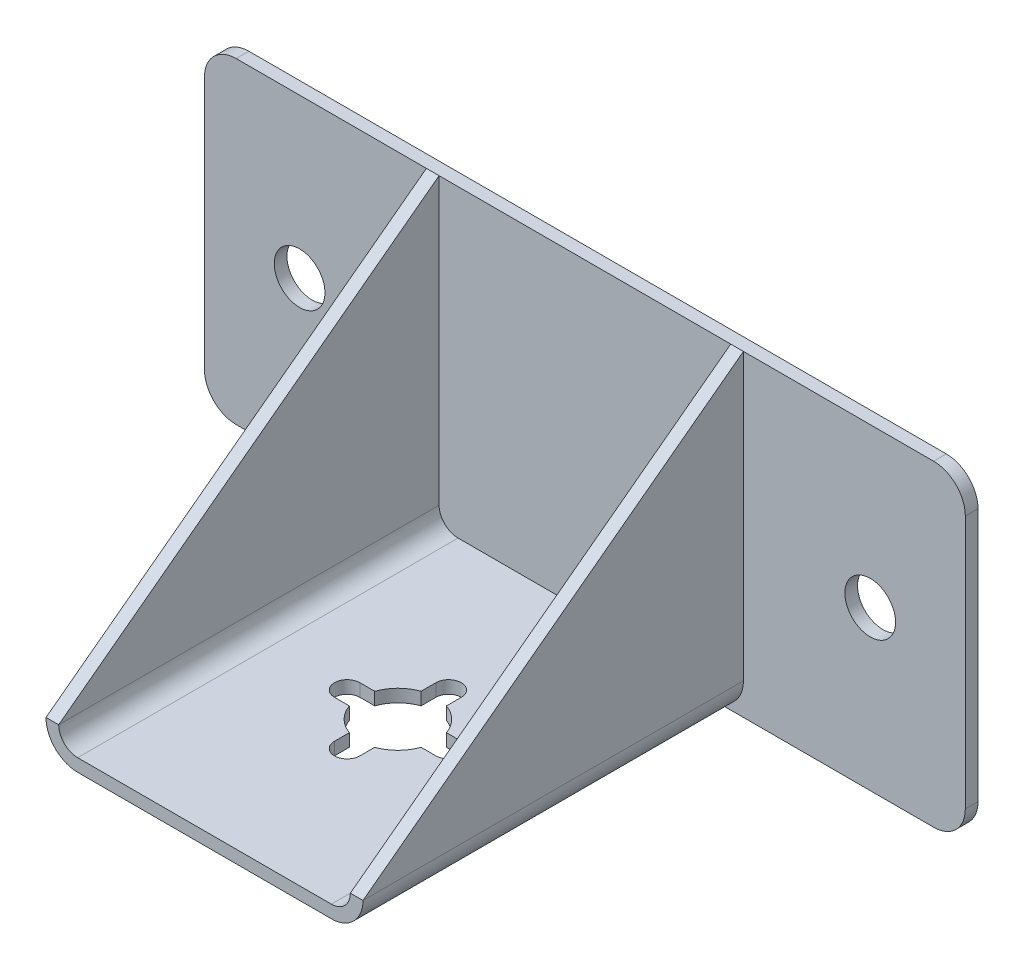
SolidWorks part; units mm, degrees
material "AISI 1020"
ref_plane "Alzado" through (0, 0, 0) normal (0, 0, 1) x (1, 0, 0)
ref_plane "Planta" through (0, 0, 0) normal (0, 1, 0) x (1, 0, 0)
ref_plane "Vista lateral" through (0, 0, 0) normal (1, 0, 0) x (0, 0, -1)
sketch "Croquis1" plane through (0, 0, 0) normal (0, 0, 1) x (1, 0, 0)
  line L1 (-55, -25) -> (55, -25)
  line L2 (-60, -20) -> (-60, 20)
  line L3 (-55, 25) -> (55, 25)
  line L4 (60, -20) -> (60, 20)
  line L5 (-60, -25) -> (60, 25) construction
  line L6 (-60, 25) -> (60, -25) construction
  arc A0 (55, 25) -> (60, 20) centre (55, 20) cw
  arc A1 (55, -25) -> (60, -20) centre (55, -20) ccw
  arc A2 (-55, -25) -> (-60, -20) centre (-55, -20) cw
  arc A3 (-60, 20) -> (-55, 25) centre (-55, 20) cw
  point P0 (0, 0)
  dimension "D3" = 5
  dimension "D1" = 120
  dimension "D2" = 50
extrude "Saliente-Extruir1" add sketch "Croquis1" along normal blind 2
sketch "Croquis2" plane through (0, 0, 2) normal (0, 0, 1) x (1, 0, 0)
  line L0 (55, 25) -> (-55, 25) construction
  line L1 (-20, -25) -> (20, -25)
  line L2 (-25, -20) -> (-25, 25)
  line L3 (-25, 25) -> (25, 25) construction
  line L4 (25, -20) -> (25, 25)
  line L5 (-25, -25) -> (25, 25) construction
  line L6 (-25, 25) -> (25, -25) construction
  line L7 (23, -20) -> (23, 25)
  line L8 (-20, -23) -> (20, -23)
  line L9 (-23, -20) -> (-23, 25)
  line L10 (-25, 25) -> (-23, 25)
  line L11 (23, 25) -> (25, 25)
  arc A0 (20, -25) -> (25, -20) centre (20, -20) ccw
  arc A1 (-20, -25) -> (-25, -20) centre (-20, -20) cw
  arc A2 (20, -23) -> (23, -20) centre (20, -20) ccw
  arc A3 (-20, -23) -> (-23, -20) centre (-20, -20) cw
  point P0 (0, 0)
  dimension "D2" = 5
  dimension "D1" = 50
  dimension "D3" = 2
extrude "Saliente-Extruir2" add sketch "Croquis2" along normal blind 60
sketch "Croquis3" plane through (25, 0, 0) normal (1, 0, 0) x (0, 0, -1)
  line L0 (-62, -20) -> (-2, 25)
  line L4 (-2, -20) -> (-2, 25)
  line L5 (-2, 25) -> (-62, 25)
  line L6 (-62, 25) -> (-62, -20)
  line L7 (-62, -20) -> (-2, -20)
  line L8 (-2, -20) -> (-2, 25)
  line L9 (-2, 25) -> (-62, 25)
  line L10 (-62, 25) -> (-62, -20)
  line L11 (-62, -20) -> (-2, -20)
  line M6 (-2, 25) -> (-62, 25)
  line M7 (-62, 25) -> (-62, -20)
  dimension "D1" = 0
extrude "Cortar-Extruir1" cut sketch "Croquis3" against normal up to surface (50 mm away) contours L0 M7 M6 up to face at (-25, 2.5, 32)
sketch "Croquis4" plane through (0, 0, 0) normal (0, 0, -1) x (-1, 0, 0)
  line L0 (-45, 0) -> (45, 0) construction
  circle A0 centre (-45, 0) radius 4
  circle A1 centre (45, 0) radius 4
  point P4 (0, 0)
  dimension "D1" = 8
  dimension "D2" = 90
extrude "Cortar-Extruir2" cut sketch "Croquis4" against normal up to surface (2 mm away) up to face at (43.3009, -3.0051, 2)
sketch "Croquis5" plane through (0, -25, 0) normal (0, -1, 0) x (1, 0, 0)
  line L0 (0, 31.5) -> (0, 23.5) construction
  line L1 (2, 23.5) -> (2, 25.8431)
  line L2 (-2, 23.5) -> (-2, 25.8431)
  line L3 (-8, 29.5) -> (-5.6569, 29.5)
  line L4 (-8, 33.5) -> (-5.6569, 33.5)
  line L5 (-2, 39.5) -> (-2, 37.1569)
  line L6 (2, 39.5) -> (2, 37.1569)
  line L7 (8, 33.5) -> (5.6569, 33.5)
  line L8 (8, 29.5) -> (5.6569, 29.5)
  circle A0 centre (0, 31.5) radius 6 construction
  circle A1 centre (0, 31.5) radius 6
  circle A2 centre (0, 23.5) radius 2
  circle A3 centre (-8, 31.5) radius 2
  circle A4 centre (0, 39.5) radius 2
  circle A5 centre (8, 31.5) radius 2
  point P14 (0, 31.5)
  point P31 (0, 31.5)
  dimension "D1" = 4
  dimension "D2" = 8
  dimension "D3" = 4
  dimension "D4" = 4
extrude "Cortar-Extruir6" cut sketch "Croquis5" against normal up to surface (2 mm away)
